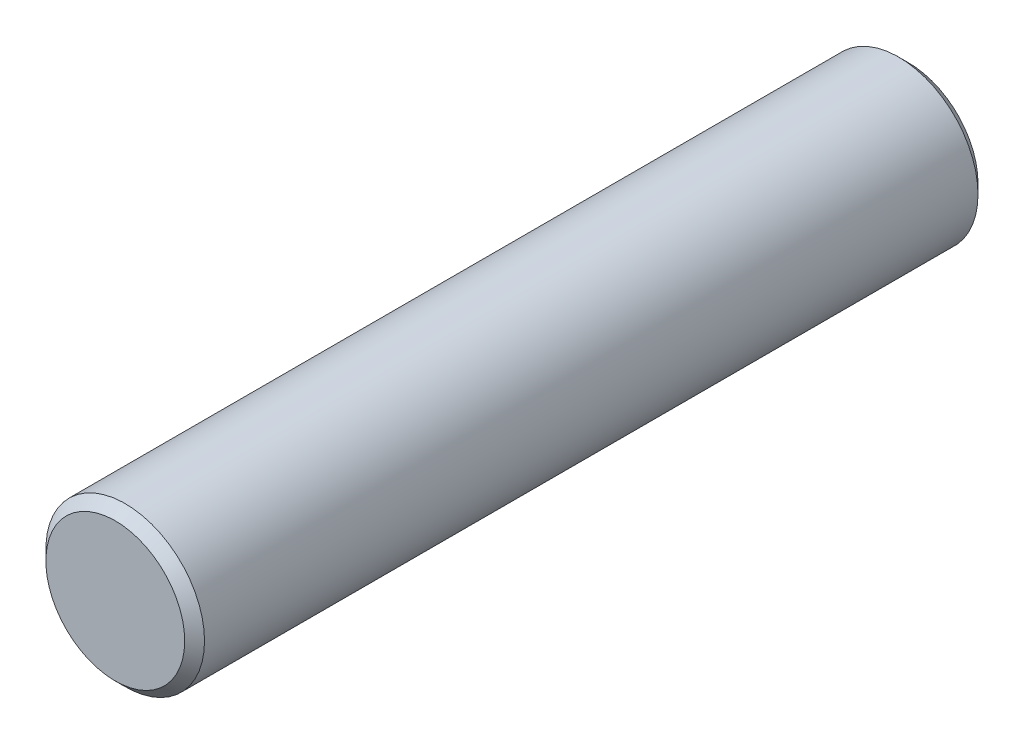
SolidWorks part; units mm, degrees
ref_plane "前基準面" through (0, 0, 0) normal (0, 0, 1) x (1, 0, 0)
ref_plane "上基準面" through (0, 0, 0) normal (0, 1, 0) x (1, 0, 0)
ref_plane "右基準面" through (0, 0, 0) normal (1, 0, 0) x (0, 0, -1)
sketch "草圖1" plane through (0, 0, 0) normal (0, 0, 1) x (1, 0, 0)
  circle A0 centre (0, 0) radius 4
  dimension "D1" = 8
extrude "填料-伸長1" add sketch "草圖1" along normal blind 40
chamfer "導角1" distance 0.5 angle 45 2 edges at (4, 0, 40) (4, 0, 0)
